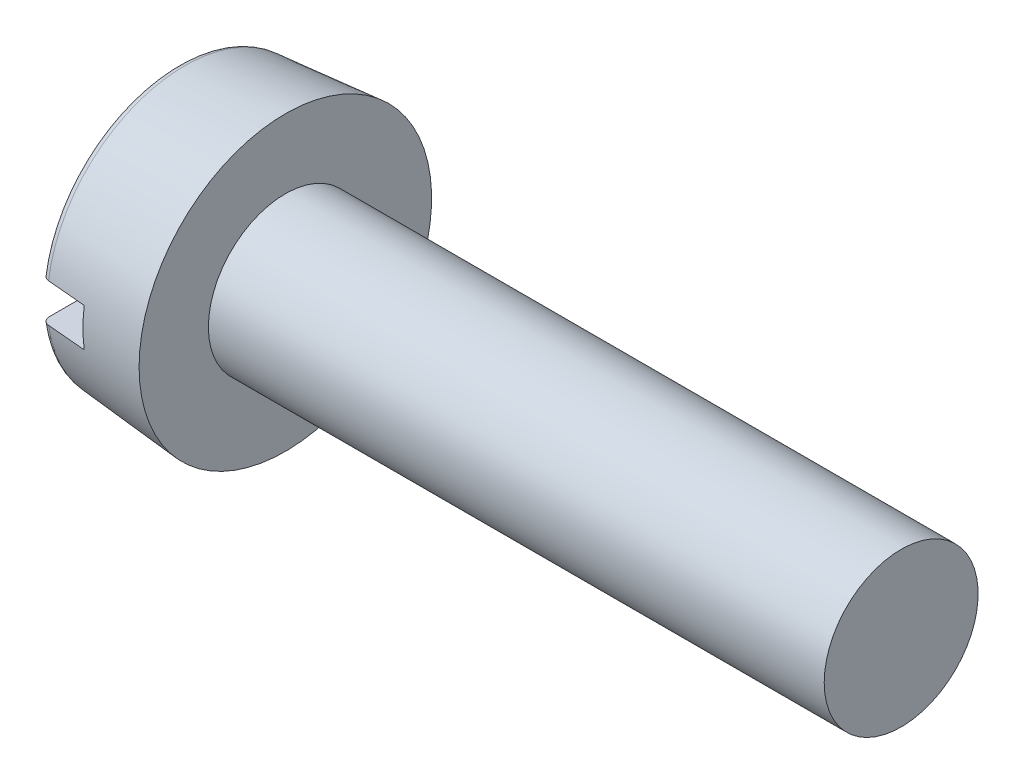
SolidWorks part; units mm, degrees
ref_plane "Plane1" through (0, 0, 0) normal (0, 0, 1) x (1, 0, 0)
ref_plane "Plane2" through (0, 0, 0) normal (0, 1, 0) x (1, 0, 0)
ref_plane "Plane3" through (0, 0, 0) normal (1, 0, 0) x (0, 0, -1)
sketch "BodySke" plane through (0, 0, 0) normal (0, 0, 1) x (1, 0, 0)
  line L0 (1.4, 1) -> (1.4, 1.9)
  line L1 (0, 0) -> (0, 1.7775)
  line L2 (-25.4, 0) -> (127, 0) construction
  line L3 (9.4, 0) -> (0, 0)
  line L4 (1.4, 1) -> (9.4, 1)
  line L5 (9.4, 1) -> (9.4, 0)
  line L6 (0, 1.7775) -> (1.4, 1.9)
  line L9 (1.8, 2.5875) -> (1.8, -6.9375) construction
  line L10 (1.4, 6.35) -> (1.4, -3.175) construction
  dimension "Length" = 8
  dimension "Head_ht" = 1.4
  dimension "Advance" = 0.4
  dimension "Thread_nom" = 8
  dimension "Head_dia" = 3.8
  dimension "Head_side_angle" = 5
  dimension "Diameter" = 2
revolve "Base-Revolve" add sketch "BodySke"
cosmetic thread "ThreadCosmetic" [suppressed]
fillet "Fillet1" [suppressed] radius 0.1
fillet "Fillet2" radius 0.1 1 edges at (0, 0, 1.7775)
sketch "Sketch2" plane through (0, 0, 0) normal (1, 0, 0) x (0, 0, -1)
  line L0 (1.9, -0.25) -> (-1.9, -0.25)
  line L1 (1.9, -0.25) -> (1.9, 0.25)
  line L2 (-1.9, 0.25) -> (1.9, 0.25)
  line L3 (-1.9, 0.25) -> (-1.9, -0.25)
  dimension "D1" = 3.8
  dimension "Slot_width" = 0.5
  dimension "D2" = 1.9
  dimension "D3" = 0.25
extrude "Slot" cut sketch "Sketch2" along normal blind 0.6
sketch "ThdSchSke" plane through (0, 0, 0) normal (0, 0, 1) x (1, 0, 0)
  line L0 (2.2, -0.774) -> (2.0418, -1)
  line L1 (2.2, -0.774) -> (2.3582, -1)
  line L2 (2.3582, -1) -> (2.3582, -1.25)
  line L3 (-3.175, 0) -> (5.1513, 0) construction
  line L5 (2.3582, -1.25) -> (2.0418, -1.25)
  line L6 (2.0418, -1.25) -> (2.0418, -1)
  dimension "Diameter" = 2
  dimension "SideAngle" = 55
  dimension "VeeAngle" = 70
  dimension "Thread_minor" = 1.548
  dimension "Overcut" = 2.5
  dimension "Start" = 2.2
revolve "ThreadSchematic" [suppressed] cut sketch "ThdSchSke" angle 360 about L3
pattern_linear "ThdSchPat" [suppressed]
equation "\"D1@Sketch2\" = \"Head_dia@BodySke\""
equation "\"D2@Sketch2\" = \"D1@Sketch2\" / 2"
equation "\"D3@Sketch2\" = \"Slot_width@Sketch2\" / 2"
equation "\"Thread_length@ThreadCosmetic\" = ((sgn( (\"Length@BodySke\" - \"Advance@BodySke\" * 2.0 ) - \"Thread_nom@BodySke\" )-1)*( (\"Length@BodySke\" - \"Advance@BodySke\"  * 2.0) - \"Thread_nom@BodySke\" ))/-2+ \"Thread_nom@BodySke\""
equation "\"Thread_minor@ThdSchSke\" = \"Thread_minor@ThreadCosmetic\""
equation "\"Diameter@ThdSchSke\" = \"Diameter@BodySke\""
equation "\"Overcut@ThdSchSke\" = \"Diameter@BodySke\" * 1.25"
equation "\"Start@ThdSchSke\" = \"Head_ht@BodySke\" + \"Length@BodySke\" - \"Thread_length@ThreadCosmetic\"  '---Non-countersunk---"
equation "\"Num_threads@ThdSchPat\" = int( \"Thread_length@ThreadCosmetic\" / \"Advance@BodySke\" + 0.999 )  + 1"
equation "\"Advance@ThdSchPat\" = \"Thread_length@ThreadCosmetic\" /  (\"Num_threads@ThdSchPat\" - 1) 'relax it"
